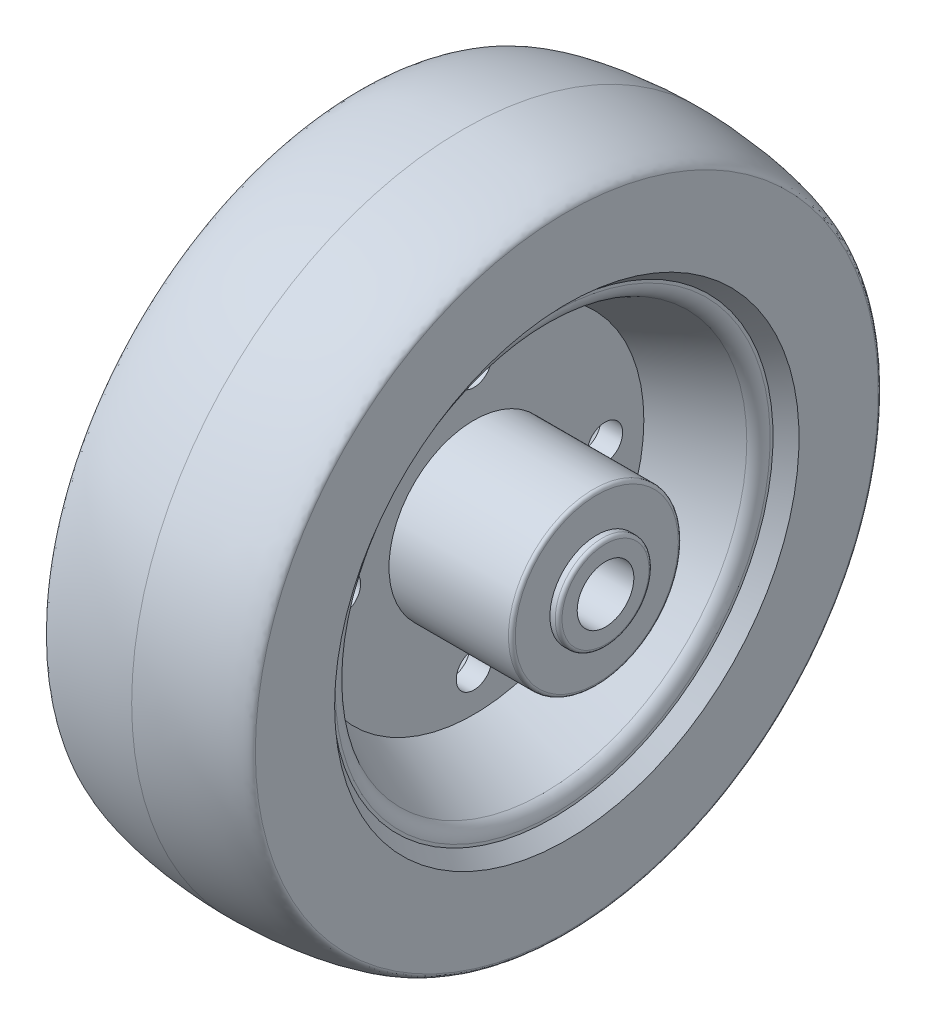
SolidWorks part; units mm, degrees
ref_plane "Front Plane" through (0, 0, 0) normal (0, 0, 1) x (1, 0, 0)
ref_plane "Top Plane" through (0, 0, 0) normal (0, 1, 0) x (1, 0, 0)
ref_plane "Right Plane" through (0, 0, 0) normal (1, 0, 0) x (0, 0, -1)
sketch "Sketch5" plane through (0, 0, 0) normal (0, 0, 1) x (1, 0, 0)
  line L0 (-23.2791, 0) -> (-23.2791, 69.85)
  line L1 (0, -1000) -> (0, 49000) construction
  line L2 (-23.2791, 0) -> (23.2791, 0) construction
  line L3 (23.2791, 0) -> (23.2791, 69.85)
  line L4 (-23.2791, 73.6345) -> (-23.2791, 66.0655) construction
  line L5 (2.3783, 74.295) -> (-2.3783, 74.295) construction
  line L6 (-23.2791, 0) -> (23.2791, 0)
  spline S0 degree 3 poles (-23.2791, 69.85) (-23.2791, 72.068) (-10.5362, 74.295) (0, 74.295) knots 0 0 0 0 1 1 1 1
  spline S1 degree 3 poles (23.2791, 69.85) (23.2791, 72.068) (10.5362, 74.295) (0, 74.295) knots 0 0 0 0 1 1 1 1
  point P8 (0, 0)
  dimension "D1" = 74.295
  dimension "D2" = 69.85
  dimension "D3" = 46.5582
revolve "Revolve1" add sketch "Sketch5" angle 360 about L6
sketch "Sketch7" plane through (0, 0, 0) normal (0, 1, 0) x (1, 0, 0)
  line L0 (-1000, 0) -> (49000, 0) construction
  line L1 (2.4511, 0) -> (2.4511, 38.1)
  line L2 (2.4511, 38.1) -> (18.0789, 45.5535)
  line L3 (20.1041, 48.7632) -> (20.1041, 49.4128)
  line L4 (20.1041, 49.4128) -> (23.2791, 52.07)
  line L5 (23.2791, -69.85) -> (23.2791, 69.85) construction
  line L6 (23.2791, 52.07) -> (23.2791, 0)
  line L7 (2.4511, 0) -> (23.2791, 0)
  arc A0 (18.0789, 45.5535) -> (20.1041, 48.7632) centre (16.5481, 48.7632) ccw
  point P12 (20.1041, 46.5194)
  dimension "D3" = 19.558
  dimension "D7" = 3.556
  dimension "D1" = 52.07
  dimension "D2" = 4.1402
  dimension "D4" = 38.1
  dimension "D5" = 20.828
  dimension "D6" = 3.175
revolve "Cut-Revolve2" cut sketch "Sketch7" angle 360 about L0
mirror "Mirror1" about plane through (0, 0, 0) normal (1, 0, 0) of "Cut-Revolve2"
sketch "Sketch8" plane through (2.4511, 0, 0) normal (1, 0, 0) x (0, 0, -1)
  circle A1 centre (0, 0) radius 19.05
  dimension "D1" = 38.1
extrude "Boss-Extrude1" add sketch "Sketch8" along normal blind 27.5463
sketch "Sketch9" plane through (29.9974, 0, 0) normal (1, 0, 0) x (0, 0, -1)
  circle A0 centre (0, 0) radius 10.5156
  dimension "D1" = 21.0312
extrude "Boss-Extrude2" add sketch "Sketch9" along normal blind 1.9558
fillet "Fillet4" radius 0.762 2 edges at (31.9532, 0, -10.5156) (29.9974, 0, -19.05)
mirror "Mirror2" about plane through (0, 0, 0) normal (1, 0, 0) of "Fillet4", "Boss-Extrude2", "Boss-Extrude1"
sketch "Sketch10" plane through (-31.9532, 0, 0) normal (-1, 0, 0) x (0, 0, 1)
  circle A0 centre (0, 0) radius 6.35
  dimension "D1" = 12.7
extrude "Cut-Extrude5" cut sketch "Sketch10" against normal through all
sketch "Sketch11" plane through (2.4511, 0, 0) normal (1, 0, 0) x (0, 0, -1)
  circle A0 centre (0, 29.3687) radius 3.9688
  circle A1 centre (0, 0) radius 6.35 construction
  circle A2 centre (29.3688, 0) radius 3.9687
  circle A3 centre (0, -29.3687) radius 3.9688
  circle A4 centre (-29.3687, 0) radius 3.9688
  dimension "D2" = 7.9375
  dimension "D1" = 29.3687
  dimension "D3" = 4
extrude "Cut-Extrude6" cut sketch "Sketch11" against normal through all
